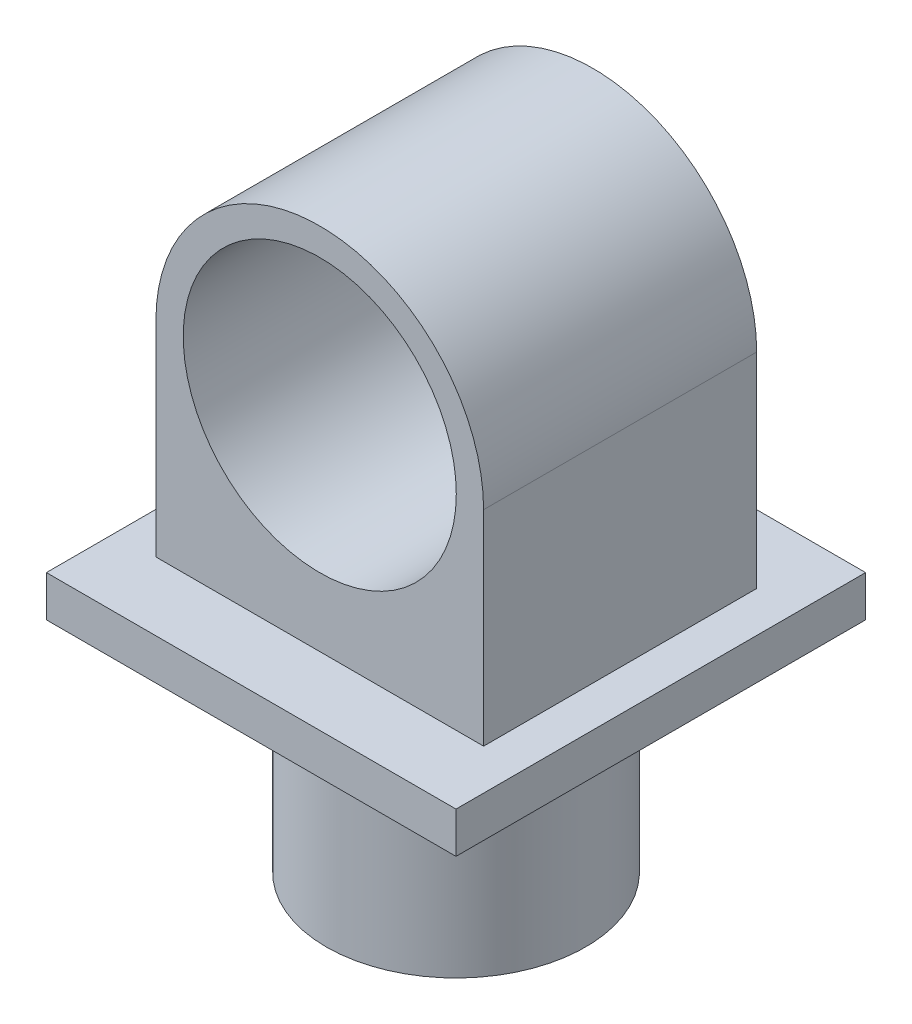
SolidWorks part; units mm, degrees
ref_plane "Front Plane" through (0, 0, 0) normal (0, 0, 1) x (1, 0, 0)
ref_plane "Top Plane" through (0, 0, 0) normal (0, 1, 0) x (1, 0, 0)
ref_plane "Right Plane" through (0, 0, 0) normal (1, 0, 0) x (0, 0, -1)
sketch "Sketch1" plane through (0, 0, 0) normal (0, 1, 0) x (1, 0, 0)
  circle A0 centre (0, 0) radius 47.5
  dimension "D1" = 95
extrude "Boss-Extrude1" add sketch "Sketch1" along normal blind 80
sketch "Sketch6" plane through (0, 80, 0) normal (0, 1, 0) x (1, 0, 0)
  line L1 (-75, -75) -> (75, -75)
  line L2 (-75, -75) -> (-75, 75)
  line L3 (-75, 75) -> (75, 75)
  line L4 (75, -75) -> (75, 75)
  line L5 (-75, -75) -> (75, 75) construction
  line L6 (-75, 75) -> (75, -75) construction
  point P0 (0, 0)
  dimension "D1" = 150
  dimension "D2" = 150
extrude "Boss-Extrude3" add sketch "Sketch6" along normal blind 15
sketch "Sketch7" plane through (0, 0, 0) normal (0, 0, 1) x (1, 0, 0)
  line L10 (-59.8909, 95) -> (60.1091, 95)
  line L11 (-59.8909, 170) -> (-59.8909, 95)
  line L12 (60.1091, 170) -> (60.1091, 95)
  circle A2 centre (0.1091, 170) radius 50
  arc A4 (-59.8909, 170) -> (60.1091, 170) centre (0.1091, 170) cw
  dimension "D1" = 100
  dimension "D2" = 60
  dimension "D3" = 75
extrude "Boss-Extrude4" add sketch "Sketch7" along normal mid plane 100
